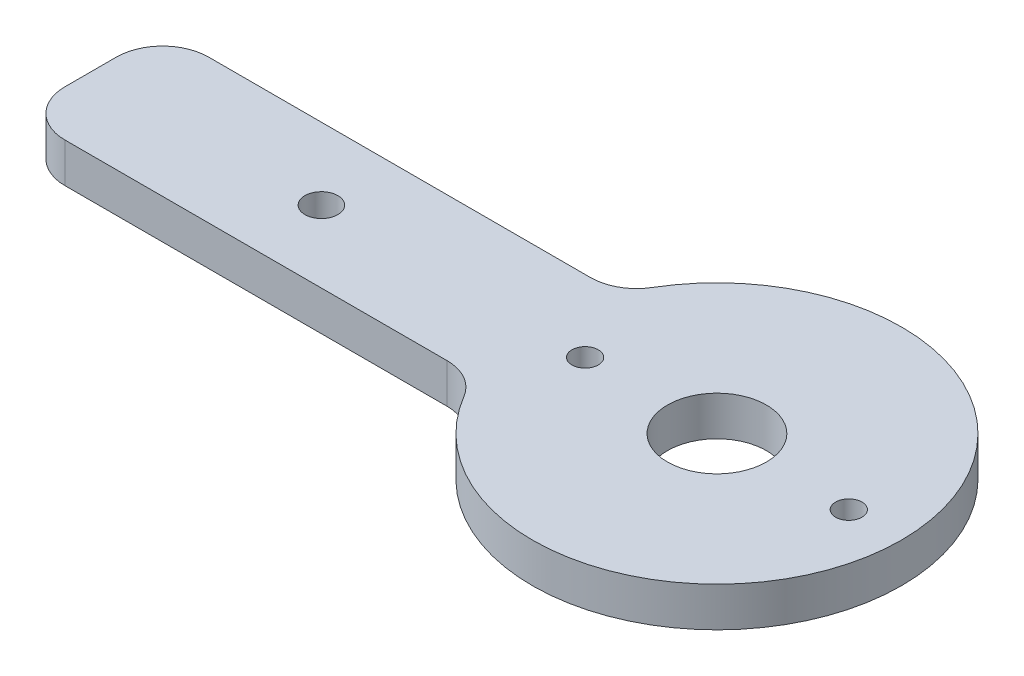
SolidWorks part; units mm, degrees
ref_plane "Plan de face" through (0, 0, 0) normal (0, 0, 1) x (1, 0, 0)
ref_plane "Plan de dessus" through (0, 0, 0) normal (0, 1, 0) x (1, 0, 0)
ref_plane "Plan de droite" through (0, 0, 0) normal (1, 0, 0) x (0, 0, -1)
sketch "Esquisse1" plane through (0, 0, 0) normal (0, 1, 0) x (1, 0, 0)
  line L1 (-74.2298, -3.895) -> (-74.2298, 3.895)
  line L2 (-67.2298, 10.895) -> (-9.3092, 10.895)
  line L12 (-67.2298, -10.895) -> (-9.3092, -10.895)
  circle A0 centre (40.7702, 0) radius 2
  circle A1 centre (20.7702, 0) radius 7.5
  circle A2 centre (0.7702, 0) radius 2
  arc A3 (-3.2933, -14.316) -> (-3.2933, 14.316) centre (20.7702, 0) ccw
  circle A4 centre (-39.2298, 0) radius 2.5
  arc A5 (-74.2298, -3.895) -> (-67.2298, -10.895) centre (-67.2298, -3.895) ccw
  arc A6 (-67.2298, 10.895) -> (-74.2298, 3.895) centre (-67.2298, 3.895) ccw
  arc A7 (-9.3092, -10.895) -> (-3.2933, -14.316) centre (-9.3092, -17.895) cw
  arc A8 (-9.3092, 10.895) -> (-3.2933, 14.316) centre (-9.3092, 17.895) ccw
  dimension "D3" = 20
  dimension "D4" = 40
  dimension "D5" = 7
  dimension "D2" = 7
  dimension "D1" = 60
extrude "Boss.-Extru.1" add sketch "Esquisse1" along normal blind 6
